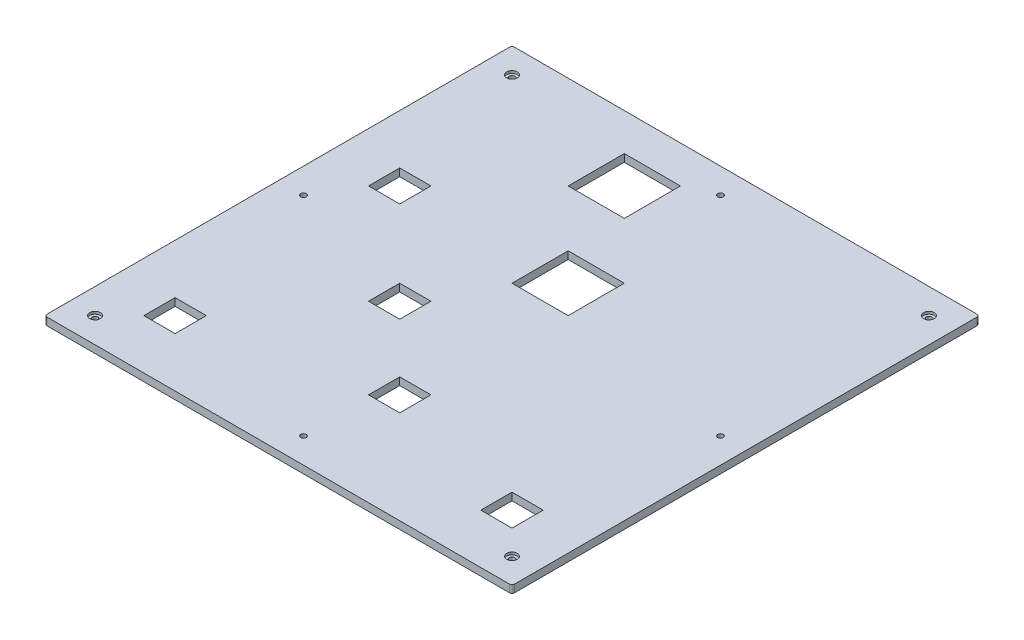
SolidWorks part; units mm, degrees
ref_plane "Plan de face" through (0, 0, 0) normal (0, 0, 1) x (1, 0, 0)
ref_plane "Plan de dessus" through (0, 0, 0) normal (0, 1, 0) x (1, 0, 0)
ref_plane "Plan de droite" through (0, 0, 0) normal (1, 0, 0) x (0, 0, -1)
sketch "Esquisse2" plane through (0, 0, 0) normal (0, 1, 0) x (1, 0, 0)
  line L1 (-92.5, 92.5) -> (92.5, 92.5)
  line L2 (-92.5, 92.5) -> (-92.5, -92.5)
  line L3 (-92.5, -92.5) -> (92.5, -92.5)
  line L4 (92.5, 92.5) -> (92.5, -92.5)
  dimension "D1" = 185
  dimension "D2" = 185
  dimension "D3" = 92.5
  dimension "D4" = 92.5
extrude "Boss.-Extru.1" add sketch "Esquisse2" against normal blind 3
sketch "Esquisse3" plane through (0, 0, 0) normal (0, 1, 0) x (1, 0, 0)
  line L0 (-77.77, 77.77) -> (77.77, 77.77)
  line L1 (-92.5, 92.5) -> (92.5, 92.5)
  line L2 (-92.5, 92.5) -> (-92.5, -92.5)
  line L3 (-92.5, -92.5) -> (92.5, -92.5)
  line L4 (92.5, 92.5) -> (92.5, -92.5)
  line L8 (77.77, 77.77) -> (77.77, -77.77)
  line L9 (-77.77, -77.77) -> (77.77, -77.77)
  line L10 (-77.77, 77.77) -> (-77.77, -77.77)
  dimension "D2" = 155.54
  dimension "D3" = 155.54
  dimension "D1" = 14.73
extrude "Boss.-Extru.2" add sketch "Esquisse3" along normal blind 40
sketch "Esquisse4" plane through (0, 0, 0) normal (0, 1, 0) x (1, 0, 0)
  line L0 (-55.55, 77.77) -> (-33.33, 77.77)
  line L1 (77.77, 77.77) -> (-77.77, 77.77) construction
  line L2 (-33.33, 77.77) -> (-33.33, 55.55)
  line L3 (-33.33, 55.55) -> (11.11, 55.55)
  line L4 (11.11, 55.55) -> (11.11, 33.33)
  line L5 (11.11, 33.33) -> (-11.11, 33.33)
  line L6 (-11.11, 33.33) -> (-11.11, -11.11)
  line L8 (-33.33, -11.11) -> (-33.33, -55.55)
  line L9 (-33.33, -55.55) -> (-55.55, -55.55)
  line L13 (-33.33, -11.11) -> (-11.11, -11.11)
  line L14 (-55.55, 77.77) -> (-55.55, 33.33)
  line L15 (-55.55, 33.33) -> (-33.33, 33.33)
  line L16 (-33.33, 33.33) -> (-33.33, 11.11)
  line L17 (-33.33, 11.11) -> (-55.55, 11.11)
  line L18 (-55.55, 11.11) -> (-55.55, -55.55)
  line L19 (-77.77, 77.77) -> (-77.77, -77.77) construction
  line L20 (-77.77, -77.77) -> (77.77, -77.77) construction
  line L21 (77.77, -77.77) -> (77.77, 77.77) construction
  line L22 (33.33, 55.55) -> (55.55, 55.55)
  line L23 (33.33, 55.55) -> (33.33, -33.33)
  line L25 (55.55, 55.55) -> (55.55, -55.55)
  line L28 (55.55, -55.55) -> (33.33, -55.55)
  line L30 (33.33, -33.33) -> (11.11, -33.33)
  line L32 (33.33, -77.77) -> (11.11, -77.77)
  line L33 (11.11, -33.33) -> (11.11, -77.77)
  line L34 (33.33, -55.55) -> (33.33, -77.77)
  line L35 (77.77, -77.77) -> (77.77, 77.77) construction
  dimension "D1" = 22.22
  dimension "D2" = 22.22
  dimension "D3" = 22.22
  dimension "D4" = 22.22
  dimension "D5" = 22.22
  dimension "D6" = 22.22
  dimension "D7" = 22.22
  dimension "D8" = 22.22
  dimension "D9" = 22.22
  dimension "D10" = 66.66
  dimension "D11" = 22.22
  dimension "D12" = 22.22
  dimension "D13" = 22.22
  dimension "D14" = 22.22
  dimension "D15" = 22.22
  dimension "D16" = 22.22
  dimension "D17" = 22.22
  dimension "D18" = 44.44
extrude "Boss.-Extru.3" add sketch "Esquisse4" along normal blind 20
sketch "Esquisse5" plane through (0, 0, 0) normal (0, 1, 0) x (1, 0, 0)
  line L0 (77.77, 77.77) -> (-33.33, 77.77) construction
  line L1 (-33.33, 55.55) -> (-11.11, 55.55)
  line L2 (-33.33, 55.55) -> (-33.33, 77.77)
  line L3 (-33.33, 77.77) -> (-11.11, 77.77)
  line L4 (-11.11, 55.55) -> (-11.11, 77.77)
  line L5 (-11.11, -11.11) -> (-11.11, 33.33) construction
  line L6 (-11.11, 33.33) -> (11.11, 33.33)
  line L7 (-11.11, 33.33) -> (-11.11, 11.11)
  line L8 (-11.11, 11.11) -> (11.11, 11.11)
  line L9 (11.11, 33.33) -> (11.11, 11.11)
  line L10 (11.11, 33.33) -> (11.11, 55.55) construction
  line L11 (-33.33, 11.11) -> (-55.55, 11.11) construction
  line L12 (33.33, -55.55) -> (55.55, -55.55) construction
  line L13 (-33.33, -11.11) -> (-20.98, -11.11)
  line L14 (-33.33, -11.11) -> (-33.33, -23.46)
  line L15 (-33.33, -23.46) -> (-20.98, -23.46)
  line L16 (-20.98, -11.11) -> (-20.98, -23.46)
  line L17 (-72.835, 28.395) -> (-60.485, 28.395)
  line L18 (-72.835, 28.395) -> (-72.835, 16.045)
  line L19 (-72.835, 16.045) -> (-60.485, 16.045)
  line L20 (-60.485, 28.395) -> (-60.485, 16.045)
  line L21 (-72.835, -60.485) -> (-60.485, -60.485)
  line L22 (-72.835, -60.485) -> (-72.835, -72.835)
  line L23 (-72.835, -72.835) -> (-60.485, -72.835)
  line L24 (-60.485, -60.485) -> (-60.485, -72.835)
  line L25 (60.485, -60.485) -> (72.835, -60.485)
  line L26 (60.485, -60.485) -> (60.485, -72.835)
  line L27 (60.485, -72.835) -> (72.835, -72.835)
  line L28 (72.835, -60.485) -> (72.835, -72.835)
  line L29 (11.11, -55.55) -> (-1.24, -55.55)
  line L30 (11.11, -55.55) -> (11.11, -43.2)
  line L31 (11.11, -43.2) -> (-1.24, -43.2)
  line L32 (-1.24, -55.55) -> (-1.24, -43.2)
  line L34 (11.11, -33.33) -> (11.11, -77.77) construction
  line L35 (-77.77, 77.77) -> (-77.77, -77.77) construction
  line L36 (-55.55, 33.33) -> (-33.33, 33.33) construction
  line L37 (-55.55, 77.77) -> (-55.55, 33.33) construction
  line L38 (-77.77, -77.77) -> (11.11, -77.77) construction
  line L39 (77.77, -77.77) -> (77.77, 77.77) construction
  dimension "D1" = 12.35
  dimension "D2" = 12.35
  dimension "D3" = 12.35
  dimension "D4" = 12.35
  dimension "D5" = 12.35
  dimension "D6" = 12.35
  dimension "D7" = 12.35
  dimension "D8" = 12.35
  dimension "D9" = 12.35
  dimension "D10" = 12.35
  dimension "D11" = 4.935
  dimension "D12" = 4.935
  dimension "D13" = 4.935
  dimension "D14" = 4.935
  dimension "D15" = 4.935
  dimension "D16" = 4.935
extrude "Enlèv. mat.-Extru.1" cut sketch "Esquisse5" against normal up to next
fillet "Congé1" radius 1 8 edges at (-92.5, 18.5, -92.5) (-92.5, 18.5, 92.5) (-92.5, 40, 0) (0, 40, 92.5) (0, 40, -92.5) (92.5, 40, 0) (92.5, 18.5, -92.5) (92.5, 18.5, 92.5)
sketch "Esquisse6" plane through (0, 40, 0) normal (0, 1, 0) x (1, 0, 0)
  line L0 (92.5, 91.5) -> (92.5, -91.5) construction
  line L1 (-91.5, 92.5) -> (91.5, 92.5) construction
  line L2 (91.5, -92.5) -> (-91.5, -92.5) construction
  line L3 (-92.5, -91.5) -> (-92.5, 91.5) construction
  circle A0 centre (-82.5, -82.5) radius 1.1
  circle A1 centre (82.5, -82.5) radius 1.1
  circle A2 centre (82.5, 82.5) radius 1.1
  circle A3 centre (-82.5, 82.5) radius 1.1
  circle A4 centre (0, 82.5) radius 1.1
  circle A5 centre (-82.5, 0) radius 1.1
  circle A6 centre (82.5, 0) radius 1.1
  circle A7 centre (0, -82.5) radius 1.1
  point P24 (0, 0)
  point P25 (0, 0)
  point P26 (0, 0)
  point P27 (0, 0)
  point P28 (0, 0)
  point P29 (0, 0)
  point P30 (0, 0)
  dimension "D1" = 2.2
  dimension "D2" = 10
  dimension "D3" = 10
  dimension "D4" = 10
  dimension "D5" = 10
  dimension "D6" = 82.5
  dimension "D7" = 82.5
extrude "Enlèv. mat.-Extru.2" cut sketch "Esquisse6" against normal through all
sketch "Esquisse7" plane through (0, 40, 0) normal (0, 1, 0) x (1, 0, 0)
  circle A0 centre (-82.5, -82.5) radius 2.1
  circle A1 centre (-82.5, 82.5) radius 2.1
  circle A2 centre (82.5, 82.5) radius 2.1
  circle A3 centre (82.5, -82.5) radius 2.1
  dimension "D1" = 4.2
extrude "Enlèv. mat.-Extru.3" cut sketch "Esquisse7" against normal blind 41
sketch "Esquisse8" plane through (0, 0, 92.5) normal (0, 0, 1) x (1, 0, 0)
  line L0 (-91.5, -3) -> (91.5, -3) construction
  line L1 (114.072, 93.7402) -> (-112.4133, 93.7402)
  line L2 (114.072, 93.7402) -> (114.072, 0)
  line L3 (114.072, 0) -> (-112.4133, 0)
  line L4 (-112.4133, 93.7402) -> (-112.4133, 0)
  dimension "D1" = 3
extrude "Enlèv. mat.-Extru.4" cut sketch "Esquisse8" against normal through all
